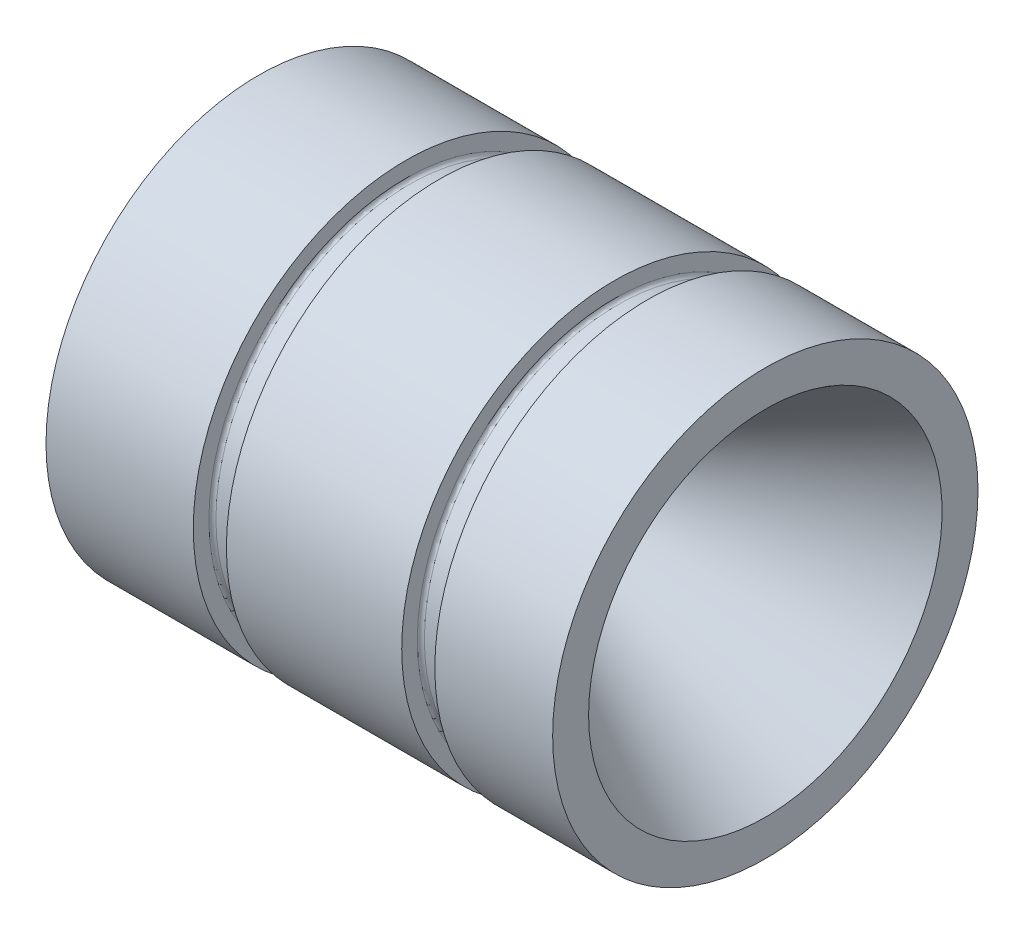
SolidWorks part; units mm, degrees
material "C (Graphite)"
ref_plane "Front Plane"
ref_plane "Top Plane" through (0, 0, 0) normal (0, 1, 0) x (1, 0, 0)
ref_plane "Right Plane" through (0, 0, 0) normal (1, 0, 0) x (0, 0, -1)
sketch "Sketch1" plane through (0, 0, 0) normal (1, 0, 0) x (0, 0, -1)
  circle A0 centre (0, 0) radius 45.847
  dimension "De" = 91.694
extrude "Boss-Extrude1" add sketch "Sketch1" along normal blind 109.22
sketch "Sketch3" plane through (0, 0, 0) normal (0, 0, 1) x (1, 0, 0)
  line L0 (0, 0) -> (311.0619, 0) construction
  line L1 (0, 0) -> (0, 28.321)
  line L2 (0, 45.847) -> (0, -45.847) construction
  line L3 (0, 28.321) -> (58.2984, 12.7)
  line L4 (58.2984, 12.7) -> (64.77, 12.7)
  line L5 (64.77, 12.7) -> (109.22, 38.1)
  line L6 (109.22, -45.847) -> (109.22, 45.847) construction
  line L7 (109.22, 38.1) -> (109.22, 0)
  line L8 (109.22, 0) -> (0, 0)
  dimension "D1" = 28.321
  dimension "D2" = 38.1
  dimension "D3" = 12.7
  dimension "D4" = 15
  dimension "D5" = 44.45
revolve "Cut-Revolve1" cut sketch "Sketch3" angle 360 about L0
imported_body "LID1"
imported_body "LID2"
sketch "Sketch4" plane through (0, 0, 0) normal (0, 0, 1) x (1, 0, 0)
  line L0 (50.4317, 0) -> (-50.4317, 0) construction
  line L1 (76.6826, 45.847) -> (83.82, 45.847)
  line L2 (76.6826, 45.847) -> (76.6826, 42.4815)
  line L3 (77.4446, 41.7195) -> (83.058, 41.7195)
  line L4 (83.82, 45.847) -> (83.82, 42.4815)
  line L5 (109.22, -45.847) -> (109.22, 45.847) construction
  line L6 (0, 45.847) -> (0, -45.847) construction
  line L7 (31.75, 45.847) -> (38.8874, 45.847)
  line L8 (31.75, 45.847) -> (31.75, 42.4815)
  line L9 (32.512, 41.7195) -> (38.1254, 41.7195)
  line L10 (38.8874, 45.847) -> (38.8874, 42.4815)
  arc A0 (83.058, 41.7195) -> (83.82, 42.4815) centre (83.058, 42.4815) ccw
  arc A1 (77.4446, 41.7195) -> (76.6826, 42.4815) centre (77.4446, 42.4815) cw
  arc A2 (38.1254, 41.7195) -> (38.8874, 42.4815) centre (38.1254, 42.4815) ccw
  arc A3 (32.512, 41.7195) -> (31.75, 42.4815) centre (32.512, 42.4815) cw
  point P8 (83.82, 41.7195)
  point P11 (76.6826, 41.7195)
  point P20 (38.8874, 41.7195)
  point P23 (31.75, 41.7195)
  dimension "D4" = 0.762
  dimension "D9" = 0.762
  dimension "D1" = 45.847
  dimension "D2" = 41.7195
  dimension "D3" = 7.1374
  dimension "D5" = 25.4
  dimension "D6" = 45.847
  dimension "D7" = 41.7195
  dimension "D8" = 7.1374
  dimension "D10" = 31.75
revolve "Cut-Revolve2" cut sketch "Sketch4" angle 360 about axis through (0, 0, 0) along (-1, 0, 0)
equation "\"De\"=3.61"
equation "\"De@Sketch1\"=\"De\""
